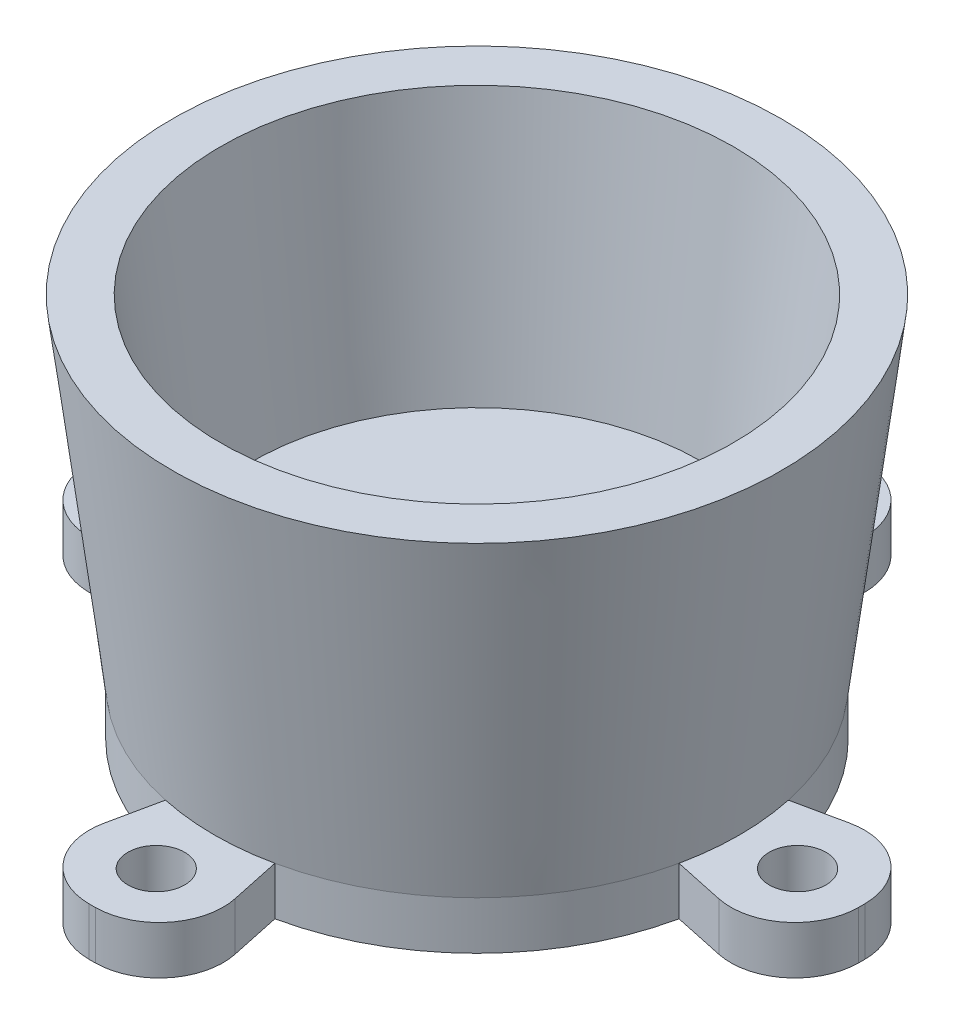
SolidWorks part; units mm, degrees
ref_plane "Front Plane" through (0, 0, 0) normal (0, 0, 1) x (1, 0, 0)
ref_plane "Top Plane" through (0, 0, 0) normal (0, 1, 0) x (1, 0, 0)
ref_plane "Right Plane" through (0, 0, 0) normal (1, 0, 0) x (0, 0, -1)
sketch "Sketch1" plane through (0, 0, 0) normal (0, 0, 1) x (1, 0, 0)
  line L0 (0, 0) -> (2.54, 20.32)
  line L1 (2.54, 20.32) -> (6.35, 20.32)
  line L2 (6.35, 20.32) -> (3.0163, -6.35)
  line L6 (0, -10.16) -> (0, -5.08)
  line L7 (0, -5.08) -> (-17.78, -5.08)
  line L8 (-17.78, -5.08) -> (-17.78, 0)
  line L9 (-17.78, 0) -> (0, 0)
  line L10 (-17.78, -5.08) -> (-17.78, -37.211) construction
  line L11 (-17.78, -37.211) -> (-17.78, 51.7958) construction
  line L12 (3.0163, -6.35) -> (12.7, -6.35)
  line L13 (12.7, -6.35) -> (12.7, -10.16)
  line L14 (12.7, -10.16) -> (0, -10.16)
  point P13 (4.445, 20.32)
  dimension "D1" = 17.78
  dimension "D2" = 20.32
  dimension "D3" = 20.32
  dimension "D4" = 26.67
  dimension "D5" = 5.08
  dimension "D6" = 3.81
  dimension "D7" = 3.81
  dimension "D8" = 12.7
  dimension "D9" = 30.48
revolve "Revolve1" add sketch "Sketch1" angle 360 about L11
sketch "Sketch2" plane through (0, -6.35, 0) normal (0, 1, 0) x (1, 0, 0)
  line L1 (12.0312, -6.35) -> (2.5599, -4.3326)
  line L2 (-17.78, 0) -> (-17.78, -82.8884) construction
  line L3 (-17.78, -82.8884) -> (-17.78, 108.6364) construction
  line L4 (-17.78, 108.6364) -> (-17.78, 0) construction
  line L5 (-17.78, 0) -> (-145.0801, 0) construction
  line L6 (-145.0801, 0) -> (144.1144, 0) construction
  line L7 (-13.4474, -20.3399) -> (-11.43, -29.8112)
  line L8 (-13.4474, 20.3399) -> (-11.43, 29.8112)
  line L9 (12.0312, 6.35) -> (2.5599, 4.3326)
  line L10 (-22.1126, -20.3399) -> (-24.13, -29.8112)
  line L11 (-47.5912, -6.35) -> (-38.1199, -4.3326)
  line L12 (-47.5912, 6.35) -> (-38.1199, 4.3326)
  line L13 (-22.1126, 20.3399) -> (-24.13, 29.8112)
  circle A0 centre (-17.78, 0) radius 20.7962 construction
  circle A1 centre (-17.78, 0) radius 30.48 construction
  arc A4 (-11.43, -29.8112) -> (12.0312, -6.35) centre (-17.78, 0) ccw
  arc A5 (-13.4474, -20.3399) -> (2.5599, -4.3326) centre (-17.78, 0) ccw
  circle A6 centre (-17.78, -25.4) radius 2.2479
  circle A7 centre (-17.78, 25.4) radius 2.2479
  arc A8 (-11.43, 29.8112) -> (12.0312, 6.35) centre (-17.78, 0) cw
  arc A9 (-13.4474, 20.3399) -> (2.5599, 4.3326) centre (-17.78, 0) cw
  arc A10 (-24.13, -29.8112) -> (-47.5912, -6.35) centre (-17.78, 0) cw
  arc A11 (-22.1126, -20.3399) -> (-38.1199, -4.3326) centre (-17.78, 0) cw
  arc A12 (-22.1126, 20.3399) -> (-38.1199, 4.3326) centre (-17.78, 0) ccw
  arc A13 (-24.13, 29.8112) -> (-47.5912, 6.35) centre (-17.78, 0) ccw
  circle A14 centre (-43.18, 0) radius 2.2479
  circle A15 centre (7.62, 0) radius 2.2479
  dimension "D1" = 6.35
  dimension "D4" = 4.4958
  dimension "D5" = 4.4958
  dimension "D6" = 4.4958
  dimension "D7" = 25.4
  dimension "D2" = 6.35
  dimension "0" = 0
  dimension "D3" = 25.4
  dimension "D8" = 25.4
extrude "Cut-Extrude1" cut sketch "Sketch2" against normal through all
fillet "Fillet1" radius 5.08 8 edges at (-24.13, -8.255, 29.8112) (-11.43, -8.255, 29.8112) (12.0312, -8.255, 6.35) (-24.13, -8.255, -29.8112) (12.0312, -8.255, -6.35) (-11.43, -8.255, -29.8112) (-47.5912, -8.255, -6.35) (-47.5912, -8.255, 6.35)
